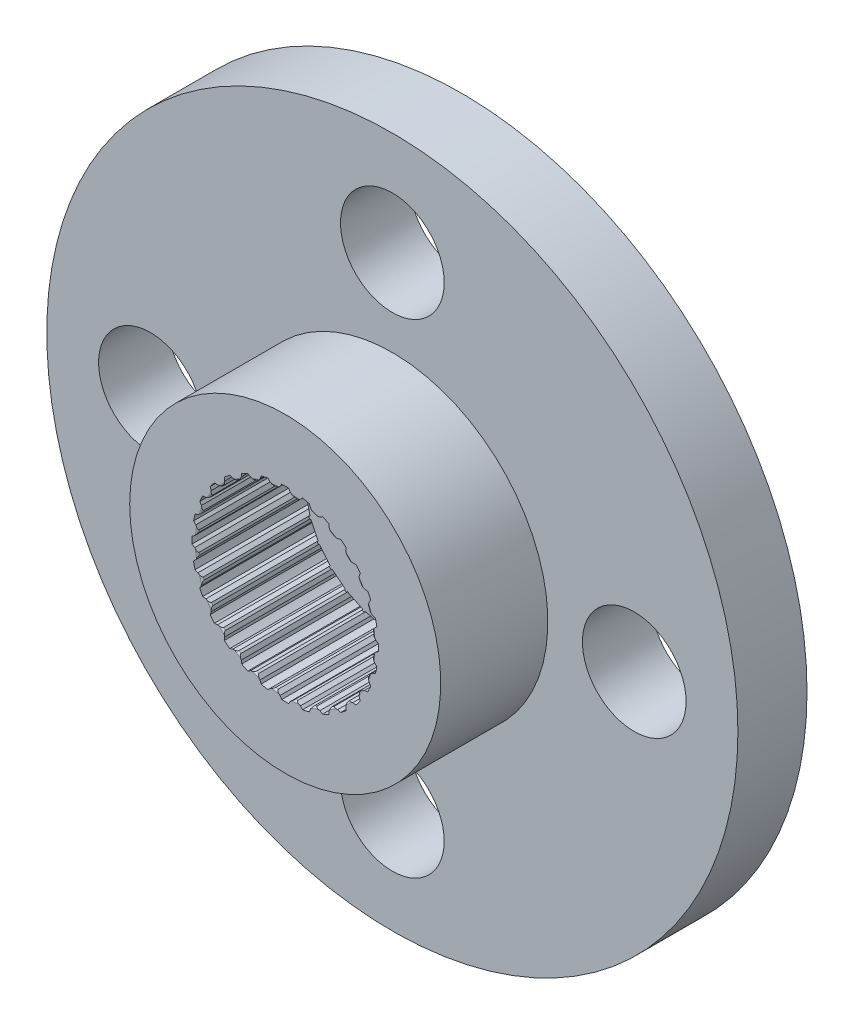
SolidWorks part; units mm, degrees
material "Beryllium"
ref_plane "Alzado" through (0, 0, 0) normal (0, 0, 1) x (1, 0, 0)
ref_plane "Planta" through (0, 0, 0) normal (0, 1, 0) x (1, 0, 0)
ref_plane "Vista lateral" through (0, 0, 0) normal (1, 0, 0) x (0, 0, -1)
sketch "Croquis1" plane through (0, 0, 0) normal (0, 0, 1) x (1, 0, 0)
  circle A0 centre (0, 0) radius 7 construction
  circle A1 centre (0, 0) radius 10
  circle A2 centre (-7, 0) radius 1.5
  circle A3 centre (0, 7) radius 1.5
  circle A4 centre (0, -7) radius 1.5
  circle A5 centre (7, 0) radius 1.5
  circle A6 centre (0, 0) radius 1.5
  dimension "D1" = 14
  dimension "D2" = 20
  dimension "D3" = 3
extrude "Saliente-Extruir1" add sketch "Croquis1" along normal blind 2
sketch "Croquis3" plane through (0, 0, 2) normal (0, 0, 1) x (1, 0, 0)
  line L0 (0, 0) -> (0, 4.1004) construction
  circle A0 centre (0, 0) radius 4.5
  circle A1 centre (0, 0) radius 2.55
  dimension "D1" = 9
  dimension "D2" = 5.1
extrude "Saliente-Extruir3" add sketch "Croquis3" along normal blind 3.1
sketch "Croquis4" plane through (0, 0, 5.1) normal (0, 0, 1) x (1, 0, 0)
  line L0 (0, 0) -> (0, 3.2695) construction
  line L1 (0.246, 2.4975) -> (-0.246, 2.4975)
  line L2 (-0.246, 2.4975) -> (-0.25, 2.5377)
  line L3 (-0.25, 2.5377) -> (-0.15, 2.62)
  line L4 (-0.15, 2.62) -> (-0.1, 2.6981)
  line L5 (0.246, 2.4975) -> (0.25, 2.5377)
  line L6 (0.25, 2.5377) -> (0.15, 2.62)
  line L7 (0.15, 2.62) -> (0.1, 2.6981)
  circle A0 centre (0, 0) radius 2.55
  circle A1 centre (0, 0) radius 2.7
  point P13 (0, 2.4975)
  point P15 (0, 2.4975)
  circle M7 centre (0, 0) radius 2.55
  dimension "D1" = 5.1
  dimension "D2" = 5.4
  dimension "D7" = 2.4975
  dimension "D3" = 0.25
  dimension "D4" = 0.15
  dimension "D5" = 0.1
  dimension "D6" = 2.62
extrude "Cortar-Extruir2" cut sketch "Croquis4" against normal blind 3.4 contours L0 A0 L6 L7 A1 | L0 A1 L4 L3 M7 | L0 L1 L5 A0 | L1 L0 L2 M7
fillet "Redondeo1" radius 0.05 1 edges at (0, -2.55, 5.1)
pattern_circular "MatrizC1" count 28 over 360 about axis through (0, 0, 0) along (0, 0, 1) of "Cortar-Extruir2"
